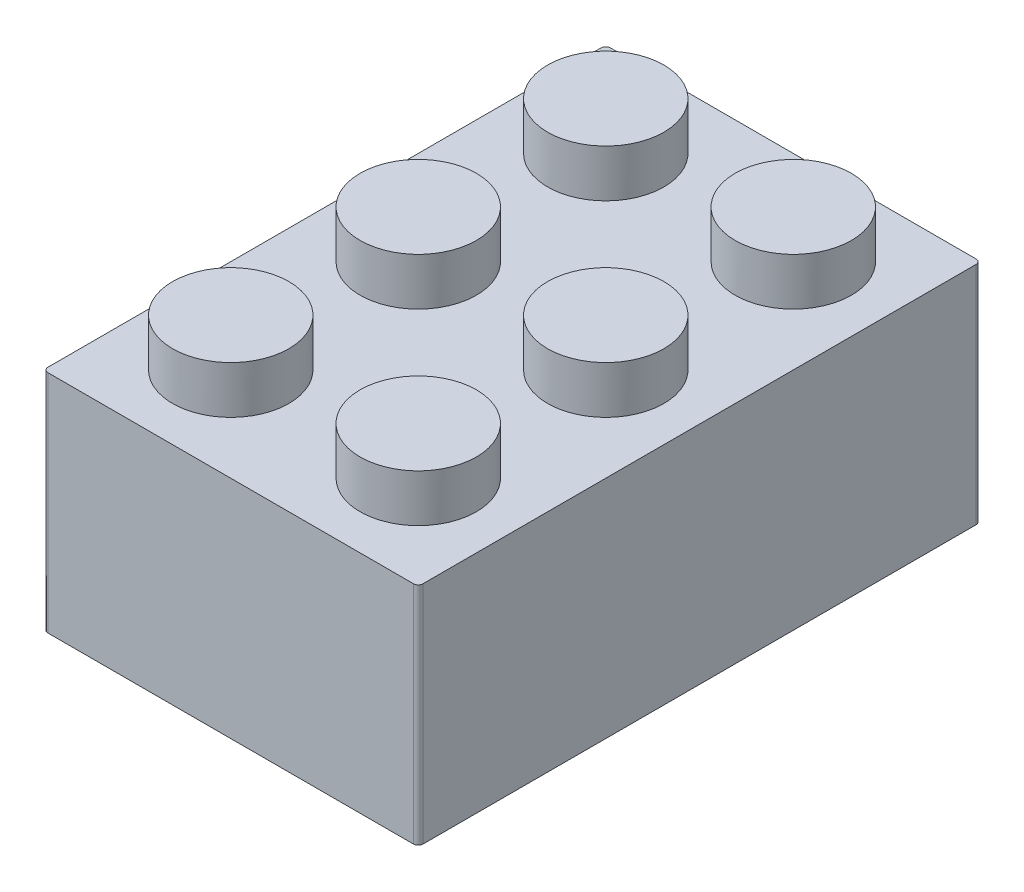
SolidWorks part; units mm, degrees
ref_plane "Front Plane" through (0, 0, 0) normal (0, 0, 1) x (1, 0, 0)
ref_plane "Top Plane" through (0, 0, 0) normal (0, 1, 0) x (1, 0, 0)
ref_plane "Right Plane" through (0, 0, 0) normal (1, 0, 0) x (0, 0, -1)
sketch "stencil" plane through (0, 0, 0) normal (0, 1, 0) x (1, 0, 0)
  line L2 (14.35, 22.25) -> (1.45, 22.25)
  line L29 (15.75, 23.65) -> (0.05, 23.65)
  line L37 (15.75, 23.65) -> (15.75, 0.05)
  line L38 (15.75, 0.05) -> (0.05, 0.05)
  line L39 (0.05, 23.65) -> (0.05, 0.05)
  line L40 (7.9, 0.05) -> (7.9, 23.65) construction
  line L41 (15.75, 11.85) -> (0.05, 11.85) construction
  line L50 (1.45, 22.25) -> (1.45, 1.45)
  line L51 (14.35, 1.45) -> (1.45, 1.45)
  line L52 (14.35, 22.25) -> (14.35, 1.45)
  circle A43 centre (3.95, 3.95) radius 2.45
  circle A44 centre (7.9, 7.9) radius 3.2
  circle A46 centre (3.95, 11.85) radius 2.45
  circle A47 centre (7.9, 15.8) radius 3.2
  circle A49 centre (3.95, 19.75) radius 2.45
  circle A50 centre (11.85, 19.75) radius 2.45
  circle A51 centre (11.85, 11.85) radius 2.45
  circle A52 centre (11.85, 3.95) radius 2.45
  circle A53 centre (7.9, 15.8) radius 2.4
  circle A54 centre (7.9, 7.9) radius 2.4
  point P1 (0, 0)
  point P6 (3.95, -15.8)
  point P9 (7.9, -15.8)
  point P10 (7.9, -11.85)
  point P13 (3.95, -7.9)
  point P15 (7.9, -7.9)
  point P17 (7.9, -3.95)
  point P18 (3.95, 0)
  point P21 (7.9, 0)
  point P25 (7.9, 3.95)
  point P27 (3.95, 7.9)
  point P28 (7.9, 7.9)
  point P29 (0, -11.85)
  point P30 (0, -7.9)
  point P31 (0, 3.95)
  point P34 (0, -3.95)
  point P35 (3.95, 0)
  point P36 (0, 15.8)
  point P37 (0, 23.7)
  point P38 (7.9, 23.7)
  point P39 (15.8, 23.7)
  point P40 (15.8, 15.8)
  point P41 (15.8, 7.9)
  point P48 (15.8, 0)
  point P49 (7.9, 0)
  point P51 (11.85, 0)
  point P52 (3.95, 3.95)
  point P53 (7.9, 3.95)
  point P55 (11.85, 3.95)
  point P56 (3.95, 7.9)
  point P57 (7.9, 7.9)
  point P58 (11.85, 7.9)
  point P59 (3.95, 11.85)
  point P60 (7.9, 11.85)
  point P61 (11.85, 11.85)
  point P64 (3.95, 15.8)
  point P65 (7.9, 15.8)
  point P66 (11.85, 15.8)
  point P68 (3.95, 19.75)
  point P69 (7.9, 19.75)
  point P70 (11.85, 19.75)
  point P71 (0, 3.95)
  point P73 (0, 7.9)
  point P75 (0, 11.85)
  point P77 (0, 15.8)
  point P79 (0, 19.75)
  point P81 (15.8, 3.95)
  point P83 (15.8, 7.9)
  point P85 (15.8, 11.85)
  point P87 (15.8, 15.8)
  point P88 (15.8, 19.75)
  point P91 (0, 23.7)
  point P93 (3.95, 23.7)
  point P94 (7.9, 23.7)
  point P95 (11.85, 23.7)
  point P96 (15.8, 23.7)
  point P97 (7.9, 11.85)
  point P118 (7.9, 11.85)
  dimension "D5" = 4.9
  dimension "D7" = 6.4
  dimension "D3" = 3.95
  dimension "D4" = 3.95
  dimension "D9" = 23.6
  dimension "D10" = 15.7
  dimension "D6" = 0.8
  dimension "D8" = 0.8
  dimension "D11" = 1.4
  dimension "D1" = 5
  dimension "D2" = 7
sketch "Sketch1" plane through (0, 0, 0) normal (0, 1, 0) x (1, 0, 0)
  line L9 (15.8, 23.7) -> (0, 23.7)
  line L10 (15.8, 23.7) -> (15.8, 0)
  line L11 (15.8, 0) -> (0, 0)
  line L12 (0, 23.7) -> (0, 0)
  line L13 (7.9, 0) -> (7.9, 23.7) construction
  line L14 (15.8, 11.85) -> (0, 11.85) construction
  point P0 (7.9, 11.85)
extrude "Boss-Extrude1" add sketch "Sketch1" along normal mid plane 9.5
sketch "Sketch2" plane through (0, 4.75, 0) normal (0, 1, 0) x (1, 0, 0)
  circle A14 centre (3.95, 3.95) radius 2.45
  circle A15 centre (11.85, 3.95) radius 2.45
  circle A16 centre (11.85, 11.85) radius 2.45
  circle A17 centre (3.95, 11.85) radius 2.45
  circle A18 centre (3.95, 19.75) radius 2.45
  circle A19 centre (11.85, 19.75) radius 2.45
  circle A20 centre (3.95, 3.95) radius 2.45 construction
extrude "Boss-Extrude2" add sketch "Sketch2" along normal blind 2
sketch "Sketch4" plane through (0, -4.75, 0) normal (0, -1, 0) x (1, 0, 0)
  line L5 (14.35, -22.25) -> (1.45, -22.25)
  line L7 (14.35, -22.25) -> (14.35, -1.45)
  line L11 (14.35, -1.45) -> (1.45, -1.45)
  line L12 (1.45, -22.25) -> (1.45, -1.45)
  line L13 (7.9, -1.45) -> (7.9, -22.25) construction
  line L14 (14.35, -11.85) -> (1.45, -11.85) construction
  point P0 (7.9, -11.85)
extrude "Cut-Extrude1" cut sketch "Sketch4" against normal blind 4
sketch "Sketch5" plane through (0, -0.75, 0) normal (0, -1, 0) x (1, 0, 0)
  circle A1 centre (7.9, -7.9) radius 2.4
  circle A5 centre (7.9, -15.8) radius 2.4
  circle A12 centre (7.9, -15.8) radius 3.2
  circle A13 centre (7.9, -7.9) radius 3.2
  circle A14 centre (7.9, -15.8) radius 2.4 construction
  circle A15 centre (7.9, -7.9) radius 3.2 construction
extrude "Boss-Extrude3" add sketch "Sketch5" along normal up to surface (4 mm away) up to face at (7.9, -4.75, -11.85)
fillet "Fillet1" radius 0.2 4 edges at (0, 0, -23.7) (15.8, 0, -23.7) (0, 0, 0) (15.8, 0, 0)
equation "\"t\"= 0.1'tolerance"
equation "\"D9@stencil\"=23.70-\"t\""
equation "\"D10@stencil\"=15.80-\"t\""
equation "\"D11@stencil\"=1.50-\"t\""
equation "\"D7@stencil\"=6.50-\"t\""
